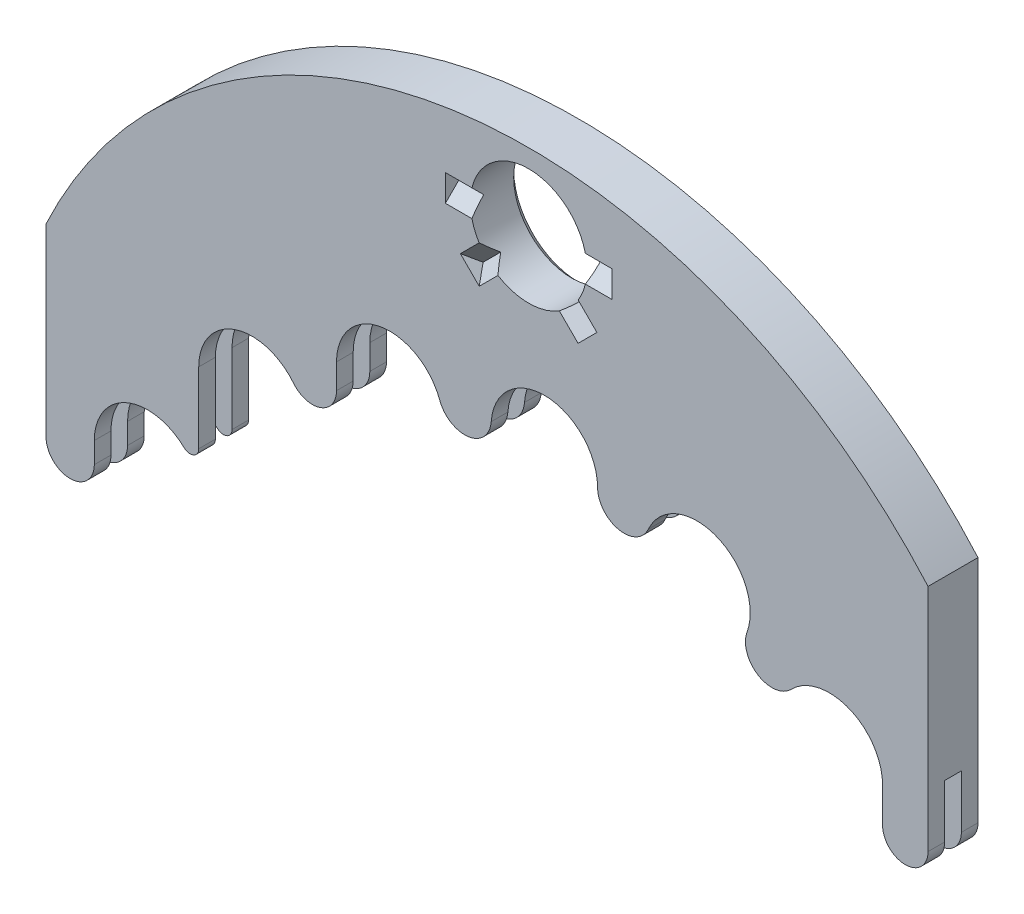
SolidWorks part; units mm, degrees
ref_plane "Front Plane" through (0, 0, 0) normal (0, 0, 1) x (1, 0, 0)
ref_plane "Top Plane" through (0, 0, 0) normal (0, 1, 0) x (1, 0, 0)
ref_plane "Right Plane" through (0, 0, 0) normal (1, 0, 0) x (0, 0, -1)
sketch "Sketch1" plane through (0, 0, 0) normal (0, 0, 1) x (1, 0, 0)
  line L1 (-13.25, -7.75) -> (13.25, -7.75)
  line L2 (-13.25, -7.75) -> (-13.25, 7.75)
  line L3 (-13.25, 7.75) -> (13.25, 7.75)
  line L4 (13.25, -7.75) -> (13.25, 7.75)
  line L5 (-13.25, -7.75) -> (13.25, 7.75) construction
  line L6 (-13.25, 7.75) -> (13.25, -7.75) construction
  point P0 (0, 0)
  dimension "D1" = 26.5
  dimension "D2" = 15.5
extrude "Boss-Extrude1" add sketch "Sketch1" along normal mid plane 1.5
sketch "Sketch2" plane through (0, 0, 0.75) normal (0, 0, 1) x (1, 0, 0)
  line L0 (-13.25, 9.75) -> (-13.25, -1.4861)
  line L3 (-13.25, 7.75) -> (-13.25, -7.75) construction
  line L4 (13.25, 7.75) -> (-13.25, 7.75) construction
  line L5 (13.25, -7.75) -> (13.25, 7.75) construction
  line L7 (13.25, 2.333) -> (13.25, 9.75)
  line L8 (13.25, 9.75) -> (-13.25, 9.75)
  line L9 (13.25, 9.75) -> (-13.25, 9.75)
  arc A0 (13.25, 2.333) -> (-13.25, -1.4861) centre (1.25, -8.25) ccw
  dimension "D1" = 14.5
  dimension "D2" = 32
  dimension "D3" = 2
extrude "Cut-Extrude1" cut sketch "Sketch2" against normal up to next
sketch "Sketch3" plane through (0, 0, 0) normal (0, 0, 1) x (1, 0, 0)
  line L0 (-13.25, -1.4861) -> (-13.25, -7.75) construction
  circle A0 centre (1.25, -13.55) radius 16
  arc A1 (13.25, 2.333) -> (-13.25, -1.4861) centre (1.25, -8.25) ccw construction
  dimension "D1" = 32
  dimension "D3" = 21.3
  dimension "D2" = 14.5
extrude "Cut-Extrude2" cut sketch "Sketch3" against normal mid plane 0.5
sketch "Sketch5" plane through (0, 0, 0.75) normal (0, 0, 1) x (1, 0, 0)
  line L0 (13.25, -7.75) -> (13.25, 2.333) construction
  circle A0 centre (1.25, -13.55) radius 13
  arc A1 (13.25, -2.967) -> (-13.25, -6.7861) centre (1.25, -13.55) ccw construction
  dimension "D1" = 26
extrude "Cut-Extrude3" cut sketch "Sketch5" against normal through all
sketch "Sketch11" plane through (0, 0, 0.75) normal (0, 0, 1) x (1, 0, 0)
  line L0 (13.25, -7.75) -> (13.25, 2.333) construction
  line L1 (11.2555, -5.25) -> (13.25, -5.25)
  line L5 (12.8844, -7.75) -> (13.25, -7.75) construction
  line L6 (13.25, -7.75) -> (13.25, -5.25)
  line L7 (12.8844, -7.75) -> (13.25, -7.75)
  arc A0 (13.25, 2.333) -> (-13.25, -1.4861) centre (1.25, -8.25) ccw construction
  arc A1 (12.8844, -7.75) -> (-10.3844, -7.75) centre (1.25, -13.55) ccw construction
  arc A2 (12.8844, -7.75) -> (11.2555, -5.25) centre (1.25, -13.55) ccw
  dimension "D1" = 13
extrude "Cut-Extrude9" cut sketch "Sketch11" against normal through all
sketch "Sketch8" plane through (0, 0, 0.75) normal (0, 0, 1) x (1, 0, 0)
  line L0 (1.25, -13.55) -> (1.25, 9.3677) construction
  circle A0 centre (1.25, 5.45) radius 1.75
  arc A4 (13.25, 2.333) -> (-13.25, -1.4861) centre (1.25, -8.25) ccw construction
  dimension "D1" = 2.3
  dimension "D2" = 3.5
extrude "Cut-Extrude6" cut sketch "Sketch8" against normal through all
sketch "Sketch4" plane through (0, 0, 0) normal (0, 0, 1) x (1, 0, 0)
  line L0 (1.25, -13.55) -> (1.25, -0.05) construction
  line L1 (1.25, -13.55) -> (1.7211, -0.0582) construction
  line L2 (1.25, -13.55) -> (6.3072, -1.033) construction
  line L3 (1.25, -13.55) -> (10.2833, -3.5175) construction
  line L4 (1.25, -13.55) -> (-2.9217, -0.7107) construction
  line L5 (1.25, -13.55) -> (-7.0614, -2.9119) construction
  line L6 (1.25, -13.55) -> (-10.1986, -6.3961) construction
  circle A0 centre (1.25, -13.55) radius 13 construction
  arc A1 (13.25, -2.967) -> (-13.25, -6.7861) centre (1.25, -13.55) ccw construction
  circle A2 centre (1.25, -13.55) radius 13.5 construction
  circle A3 centre (1.7211, -0.0582) radius 1.6
  circle A4 centre (6.3072, -1.033) radius 1.6
  circle A5 centre (10.2833, -3.5175) radius 1.6
  circle A6 centre (-2.9217, -0.7107) radius 1.6
  circle A7 centre (-7.0614, -2.9119) radius 1.6
  circle A8 centre (-10.1986, -6.3961) radius 1.6
  dimension "D1" = 26
  dimension "D6" = 3.2
  dimension "D7" = 18
  dimension "D3" = 2
  dimension "D4" = 22
  dimension "D5" = 42
  dimension "D8" = 38
  dimension "D9" = 58
  dimension "D2" = 0.5
extrude "Cut-Extrude7" cut sketch "Sketch4" against normal through all both and the other way through all
sketch "Sketch9" plane through (0, 0, 0.75) normal (0, 0, 1) x (1, 0, 0)
  line L0 (-11.7986, -6.3961) -> (-11.7986, -7.0243)
  line L1 (-13.25, -1.4861) -> (-13.25, -7.75) construction
  line L2 (-13.25, -7.75) -> (-11.0512, -7.75) construction
  line L3 (-13.25, -7.0243) -> (-13.25, -8.25)
  line L5 (-11.0512, -7.75) -> (-11.0512, -8.25)
  line L6 (-13.25, -8.25) -> (-11.0512, -8.25)
  line L7 (-13.25, -8.25) -> (-11.0512, -8.25)
  arc A0 (-8.913, -5.4436) -> (-11.0512, -7.75) centre (-10.1986, -6.3961) ccw construction
  arc A1 (-11.7986, -6.3961) -> (-11.0512, -7.75) centre (-10.1986, -6.3961) ccw
  arc A2 (-13.25, -7.0243) -> (-11.7986, -7.0243) centre (-12.5243, -7.0243) ccw
  dimension "D1" = 0.5
extrude "Cut-Extrude8" cut sketch "Sketch9" against normal through all
sketch "Sketch12" plane through (0, 0, 0.75) normal (0, 0, 1) x (1, 0, 0)
  line L0 (11.8833, -3.5175) -> (11.8833, -4.5666)
  line L1 (13.25, -5.25) -> (11.2555, -5.25) construction
  line L2 (13.25, -5.25) -> (13.25, 2.333) construction
  line L4 (13.25, -5.75) -> (13.25, -4.5666)
  line L5 (13.25, -5.75) -> (11.2555, -5.75)
  line L6 (11.2555, -5.25) -> (11.2555, -5.75)
  arc A0 (10.998, -4.949) -> (8.7849, -2.9564) centre (10.2833, -3.5175) ccw construction
  arc A1 (11.8833, -4.5666) -> (13.25, -4.5666) centre (12.5666, -4.5666) ccw
  arc A2 (11.2555, -5.25) -> (10.998, -4.949) centre (1.25, -13.55) ccw construction
  arc A3 (10.998, -4.949) -> (11.8833, -3.5175) centre (10.2833, -3.5175) ccw
  arc A4 (11.2555, -5.25) -> (10.998, -4.949) centre (1.25, -13.55) ccw
  dimension "D1" = 0.5
extrude "Cut-Extrude10" cut sketch "Sketch12" against normal through all contours L5 L6 A4 A3 L0 A1 L4
sketch "Sketch13" plane through (0, 0, 0.75) normal (0, 0, 1) x (1, 0, 0)
  line L0 (-8.6614, -2.9119) -> (-8.6614, -5.0428)
  line L1 (-4.5217, -0.7107) -> (-4.5217, -1.4604)
  line L2 (11.8833, -3.5175) -> (11.8833, -4.5666) construction
  line L3 (11.8833, -3.5175) -> (11.8833, -6.9786)
  arc A0 (7.8117, -1.5776) -> (9.1343, -2.4041) centre (8.5616, -1.849) ccw
  arc A1 (7.4684, -2.1337) -> (4.7073, -1.0181) centre (6.3072, -1.033) ccw construction
  arc A2 (11.8833, -3.5175) -> (8.7849, -2.9564) centre (10.2833, -3.5175) ccw construction
  arc A3 (8.7849, -2.9564) -> (7.4684, -2.1337) centre (1.25, -13.55) ccw construction
  arc A4 (3.1888, -0.6954) -> (0.2126, -0.5915) centre (1.7211, -0.0582) ccw construction
  arc A5 (-1.3247, -0.8075) -> (-4.1569, -1.7278) centre (-2.9217, -0.7107) ccw construction
  arc A6 (-5.5276, -2.4566) -> (-7.8743, -4.29) centre (-7.0614, -2.9119) ccw construction
  arc A7 (-8.913, -5.4436) -> (-11.7986, -6.3961) centre (-10.1986, -6.3961) ccw construction
  arc A8 (11.8833, -3.5175) -> (9.1343, -2.4041) centre (10.2833, -3.5175) ccw
  arc A9 (7.8117, -1.5776) -> (4.8467, -0.3797) centre (6.3072, -1.033) ccw
  arc A10 (3.3211, -0.0554) -> (0.1252, 0.0562) centre (1.7211, -0.0582) ccw
  arc A11 (-1.4192, -0.1608) -> (-4.5217, -0.7107) centre (-2.9217, -0.7107) ccw
  arc A12 (-5.8117, -1.9127) -> (-8.6614, -2.9119) centre (-7.0614, -2.9119) ccw
  arc A13 (-8.6655, -5.9386) -> (-9.1007, -5.2323) centre (-10.1986, -6.3961) ccw
  arc A16 (3.3211, -0.0554) -> (4.8467, -0.3797) centre (4.1187, -0.054) ccw
  arc A17 (4.5743, -1.5001) -> (3.1142, -1.1898) centre (1.25, -13.55) ccw
  arc A18 (11.8833, -6.9786) -> (-8.6655, -5.9386) centre (1.25, -13.55) ccw
  arc A19 (4.7073, -1.0181) -> (3.1888, -0.6954) centre (1.25, -13.55) ccw construction
  arc A20 (-1.4192, -0.1608) -> (0.1252, 0.0562) centre (-0.6702, 0.1133) ccw
  arc A21 (0.2126, -0.5915) -> (-1.3247, -0.8075) centre (1.25, -13.55) ccw construction
  arc A22 (-9.1007, -5.2323) -> (-8.6614, -5.0428) centre (-8.9219, -5.0428) ccw
  arc A24 (-7.8743, -4.29) -> (-8.913, -5.4436) centre (1.25, -13.55) ccw construction
  arc A26 (-5.8117, -1.9127) -> (-4.5217, -1.4604) centre (-5.246, -1.4604) ccw
  arc A27 (-4.1569, -1.7278) -> (-5.5276, -2.4566) centre (1.25, -13.55) ccw construction
  dimension "D1" = 0.5
extrude "Cut-Extrude11" cut sketch "Sketch13" against normal through all
chamfer "Chamfer1" distance 0.2 angle 45 1 edges at (3, 5.45, -0.75)
ref_plane "Plane1" through (1.25, 0, 0) normal (-1, 0, 0) x (0, 0, 1)
sketch "Sketch14" plane through (1.25, 0, 0) normal (-1, 0, 0) x (0, 0, 1)
  line L0 (-0.55, 5.45) -> (1.3969, 5.45) construction
  line L1 (-0.55, 7.2) -> (-0.55, 3.7) construction
  line L2 (0.75, 5.85) -> (0.35, 5.45)
  line L3 (0.75, -1.4861) -> (0.75, 7.75) construction
  line L4 (0.35, 5.45) -> (0.75, 5.05)
  line L5 (0.75, 5.05) -> (0.75, 5.85)
  dimension "D1" = 0.4
extrude "Cut-Extrude12" cut sketch "Sketch14" along normal blind 2.5 contours L2 L4 L5
pattern_circular "CirPattern1" count 2 over 45 about axis through (1.25, 5.45, 0) along (0, 0, 1) of "Cut-Extrude12"
mirror "Mirror1" about plane through (1.25, 0, 0) normal (-1, 0, 0) of "CirPattern1", "Cut-Extrude12"
